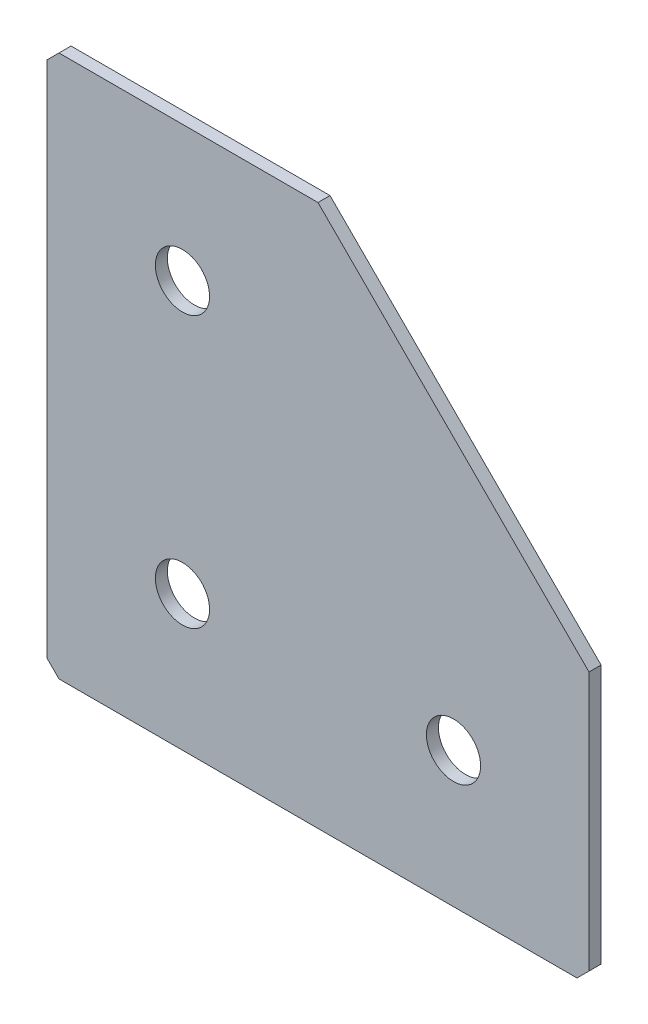
SolidWorks part; units mm, degrees
material "Простая углеродистая сталь"
ref_plane "Спереди(Плоскость XY)" through (0, 0, 0) normal (0, 0, 1) x (1, 0, 0)
ref_plane "Сверху(Плоскость XZ)" through (0, 0, 0) normal (0, 1, 0) x (1, 0, 0)
ref_plane "Справа(Плоскость ZY)" through (0, 0, 0) normal (1, 0, 0) x (0, 0, -1)
sketch "Эскиз1" plane through (0, 0, 0) normal (0, 0, -1) x (1, 0, 0)
  line L0 (0, 0) -> (0, 90)
  line L1 (0, 90) -> (90, 90)
  line L2 (90, 90) -> (90, 45)
  line L3 (90, 45) -> (45, 45) construction
  line L4 (45, 45) -> (45, 0) construction
  line L5 (45, 0) -> (0, 0)
  line L6 (90, 45) -> (45, 0)
  dimension "D1" = 90
  dimension "D2" = 45
  dimension "D3" = 45
  dimension "D4" = 45
extrude "Бобышка-Вытянуть1" add sketch "Эскиз1" along normal blind 2
hole_wizard "Отверстие с зазором M81" positions "Эскиз2" profile "Эскиз3" hole size "M8" standard "DIN" end condition through all
sketch "Эскиз2" plane through (0, 0, -2) normal (0, 0, -1) x (1, 0, 0)
  line L1 (0, 0) -> (45, 0) construction
  line L6 (0, 90) -> (0, 0) construction
  point P4 (22.5, 67.5)
  point P6 (22.5, 22.5)
  point P29 (67.5, 67.5)
  dimension "D1" = 45
  dimension "D2" = 45
  dimension "D4" = 22.5
  dimension "D5" = 22.5
sketch "Эскиз3" plane through (22.5, -67.5, -2) normal (1, 0, 0) x (0, 1, 0)
  line L0 (0, 0) -> (0, 2)
  line L1 (0, 2) -> (4.5, 2)
  line L2 (4.5, 2) -> (4.5, 0)
  line L5 (4.5, 0) -> (0, 0)
  line L11 (0, -6.35) -> (0, 107.95) construction
  dimension "Диаметр сквозного отверстия" = 9
  dimension "Глубина сквозного отверстия" = 2
chamfer "Фаска1" distance 2 angle 45 3 edges at (0, 0, -1) (90, -90, -1) (0, -90, -1)
